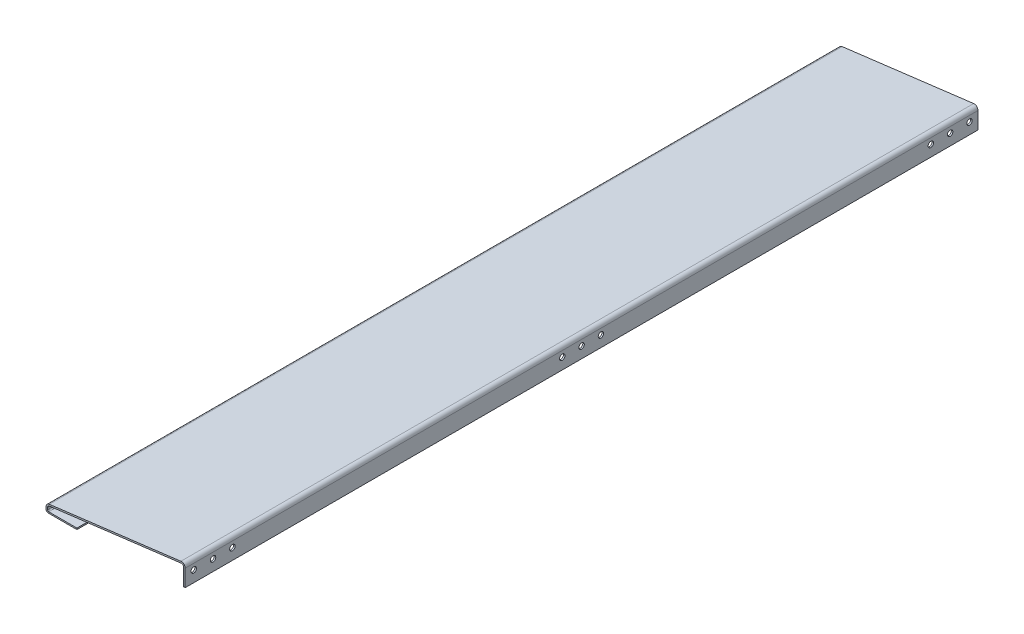
SolidWorks part; units mm, degrees
material "普通碳钢"
ref_plane "前视基准面" through (0, 0, 0) normal (0, 0, 1) x (1, 0, 0)
ref_plane "上视基准面" through (0, 0, 0) normal (0, 1, 0) x (1, 0, 0)
ref_plane "右视基准面" through (0, 0, 0) normal (1, 0, 0) x (0, 0, -1)
sketch "草图1" plane through (0, 0, 0) normal (0, 0, 1) x (1, 0, 0)
  line L0 (0, 0) -> (0, 43.6722)
  line L1 (-11.2403, 53.595) -> (-351.2403, 11.095)
  line L2 (-360, 1.1722) -> (-360, -20) construction
  line L4 (-360, -10) -> (-300, -10)
  line L5 (-360, 1.1722) -> (-360, -10)
  line L6 (-300, -10) -> (0, 0)
  arc A0 (-360, 1.1722) -> (-351.2403, 11.095) centre (-350, 1.1722) cw
  arc A1 (0, 43.6722) -> (-11.2403, 53.595) centre (-10, 43.6722) ccw
  point P8 (-360, 10)
  point P11 (0, 55)
  dimension "D5" = 10
  dimension "D6" = 10
  dimension "D1" = 55
  dimension "D2" = 360
  dimension "D3" = 30
  dimension "D4" = 20
  dimension "D7" = 60
  dimension "D8" = 10
extrude "凸台-拉伸1" add sketch "草图1" along normal blind 2050
shell "抽壳1" thickness 4
sketch "草图2" plane through (0, 0, 0) normal (1, 0, 0) x (0, 0, -1)
  line L0 (0, 53.6722) -> (-2050, 53.6722) construction
  line L1 (-2050, 0) -> (-2050, 43.6722) construction
  line L2 (-2035, 28.6722) -> (-959.231, 28.6722) construction
  line L3 (-1025, 43.6722) -> (-1025, -321.4929) construction
  line L4 (-2050, 43.6722) -> (0, 43.6722) construction
  line L5 (-15, 28.6722) -> (-1090.769, 28.6722) construction
  circle A0 centre (-2028, 28.6722) radius 7
  circle A1 centre (-1978, 28.6722) radius 7
  circle A2 centre (-1928, 28.6722) radius 7
  circle A3 centre (-122, 28.6722) radius 7
  circle A4 centre (-72, 28.6722) radius 7
  circle A5 centre (-22, 28.6722) radius 7
  circle A6 centre (-1025, 28.6722) radius 7
  circle A7 centre (-1075, 28.6722) radius 7
  circle A8 centre (-975, 28.6722) radius 7
  dimension "D1" = 14
  dimension "D4" = 50
  dimension "D6" = 14
  dimension "D7" = 14
  dimension "D8" = 50
  dimension "D10" = 14
  dimension "D11" = 14
  dimension "D12" = 14
  dimension "D2" = 25
  dimension "D3" = 22
  dimension "D5" = 50
  dimension "D9" = 50
extrude "切除-拉伸1" cut sketch "草图2" against normal up to next
sketch "草图3" plane through (0, 0, 2050) normal (0, 0, 1) x (1, 0, 0)
  line L1 (-360, -10) -> (-280, -10)
  line L2 (-360, -10) -> (-360, -6.5)
  line L3 (-360, -6.5) -> (-280, -6.5)
  line L4 (-280, -10) -> (-280, -6.5)
  dimension "D1" = 3.5
  dimension "D2" = 80
extrude "凸台-拉伸2" add sketch "草图3" against normal up to vertex (2050 mm away) up to point (-356, -10, 0)
fillet "圆角1" radius 3 1 edges at (-356, -6.5, 1025)
fillet "圆角2" radius 6.5 1 edges at (-360, -10, 1025)
